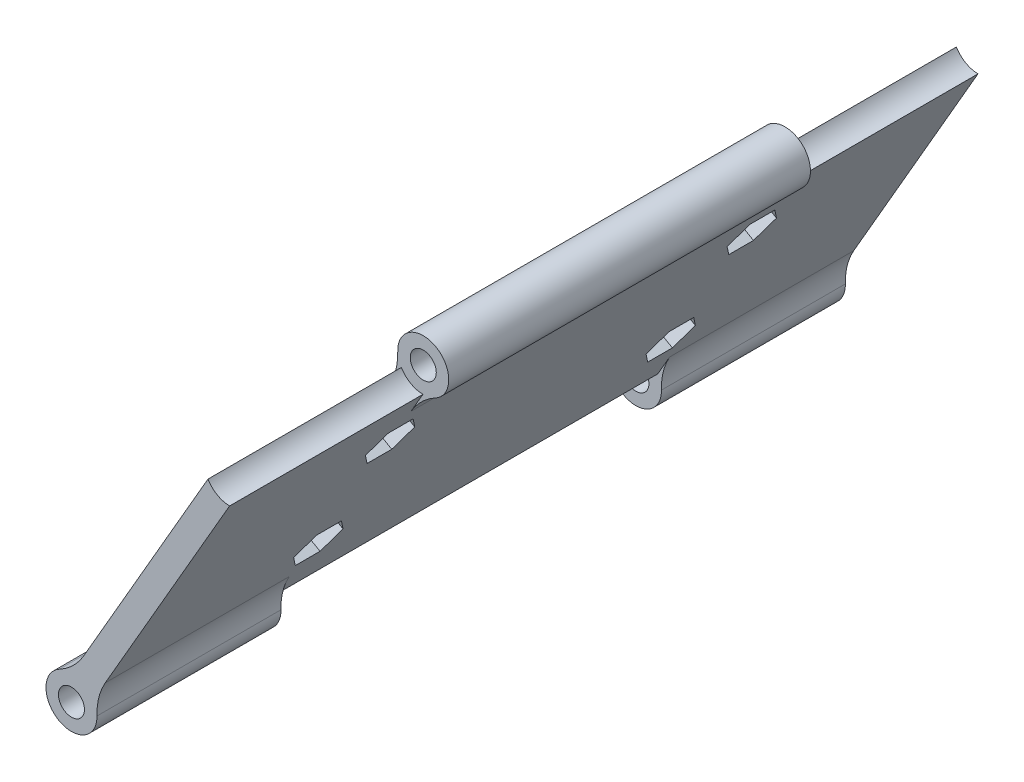
SolidWorks part; units mm, degrees
material "PLA"
ref_plane "Front Plane" through (0, 0, 0) normal (0, 0, 1) x (1, 0, 0)
ref_plane "Top Plane" through (0, 0, 0) normal (0, 1, 0) x (1, 0, 0)
ref_plane "Right Plane" through (0, 0, 0) normal (1, 0, 0) x (0, 0, -1)
sketch "Sketch2" plane through (0, 0, 0) normal (0, 0, 1) x (1, 0, 0)
  line L0 (0, 0) -> (38.1, 0)
  line L1 (0, 0) -> (0, -38.1)
  circle A0 centre (0, 0) radius 38.1
  circle A1 centre (0, -29.337) radius 1.5875
  circle A2 centre (-25.4066, 14.6685) radius 1.5875
  circle A3 centre (25.4066, 14.6685) radius 1.5875
  point P13 (0, 0)
  dimension "D1" = 76.2
  dimension "D2" = 3.175
  dimension "D3" = 8.763
  dimension "D4" = 3
extrude "Boss-Extrude1" add sketch "Sketch2" along normal blind 10 contours A1 L1 L0 A0 A3 A2 | A1 L1 A0 L0
sketch "Sketch3" plane through (0, 0, 10) normal (0, 0, 1) x (1, 0, 0)
  line L1 (0, -29.337) -> (25.4066, 14.6685)
  line L2 (1.7321, -30.337) -> (27.1386, 13.6685)
  line L3 (-1.7321, -28.337) -> (23.6745, 15.6685)
  circle A11 centre (0, -29.337) radius 1.5875
  circle A12 centre (25.4066, 14.6685) radius 1.5875
  circle A17 centre (0, -29.337) radius 2.0875
  circle A18 centre (25.4066, 14.6685) radius 2.0875
  circle A19 centre (0, -29.337) radius 4.0875
  circle A20 centre (25.4066, 14.6685) radius 4.0875
  dimension "D1" = 0.5
  dimension "D2" = 2
  dimension "D4" = 2
  dimension "D5" = 2
extrude "Boss-Extrude2" add sketch "Sketch3" along normal blind 120 separate body contours L2 A20 L3 A18 | L1 A20 L2 A18 | L3 A20 L1 A18 | A20 L1 A19 L2 | A20 L3 A19 L1 | L1 A19 L3 A17 | L2 A19 L1 A17 | L3 A19 L2 A17
delete or keep bodies "Body-Delete/Keep 2" type delete bodies bodies 101
ref_plane "Plane1" through (0, 0, 70) normal (0, 0, 1) x (1, 0, 0)
sketch "Sketch4" plane through (0, 0, 70) normal (0, 0, 1) x (1, 0, 0)
  circle A1 centre (0, -29.337) radius 4.0875
extrude "Cut-Extrude1" cut sketch "Sketch4" against normal blind 30.5 and the other way blind 30.5
sketch "Sketch5" plane through (0, 0, 10) normal (0, 0, -1) x (-1, 0, 0)
  circle A0 centre (-25.4066, 14.6685) radius 4.0875
extrude "Cut-Extrude2" cut sketch "Sketch5" against normal offset from surface (31 mm away) 1.5 up to face at (2.0875, -29.337, 39.5) offset beyond the face yes
sketch "Sketch6" plane through (0, 0, 130) normal (0, 0, 1) x (1, 0, 0)
  circle A0 centre (25.4066, 14.6685) radius 4.0875
extrude "Cut-Extrude3" cut sketch "Sketch6" against normal offset from surface (31 mm away) 1.5 contours A0 up to face at (2.0875, -29.337, 100.5) offset beyond the face yes
fillet "Fillet1" radius 10 6 edges at (21.8921, 12.5813, 70) (0.0503, -25.2498, 24.75) (0.0503, -25.2498, 115.25) (3.5144, -27.2498, 115.25) (3.5144, -27.2498, 24.75) (25.3562, 10.5813, 70)
sketch "Sketch7" plane through (10.9712, -6.3342, 0) normal (-0.866, 0.5, 0) x (0, 0, 1)
  circle A0 centre (40.9814, 11.2661) radius 1.5
  circle A1 centre (42.4851, -11.7339) radius 1.5
  circle A2 centre (98.9814, -11.7339) radius 1.5
  circle A3 centre (98.9814, 11.2661) radius 1.5
  circle A4 centre (40.9814, 11.2661) radius 2
  circle A5 centre (42.4851, -11.7339) radius 2
  circle A6 centre (98.9814, -11.7339) radius 2
  circle A7 centre (98.9814, 11.2661) radius 2
  dimension "D1" = 0.5
extrude "Cut-Extrude4" cut sketch "Sketch7" against normal up to surface (4 mm away) contours A4 | A7 | A6 | A5 up to face at (14.7532, -7.7836, 70)
sketch "Sketch8" plane through (14.4353, -8.3342, 0) normal (0.866, -0.5, 0) x (0, 0, -1)
  line L1 (-37.0219, 11.2661) -> (-39.0016, 14.6951)
  line L2 (-39.0016, 14.6951) -> (-42.9611, 14.6951)
  line L3 (-42.9611, 14.6951) -> (-44.9408, 11.2661)
  line L4 (-44.9408, 11.2661) -> (-42.9611, 7.8371)
  line L5 (-42.9611, 7.8371) -> (-39.0016, 7.8371)
  line L6 (-39.0016, 7.8371) -> (-37.0219, 11.2661)
  line L7 (-38.5256, -11.7339) -> (-40.5053, -8.3049)
  line L8 (-40.5053, -8.3049) -> (-44.4648, -8.3049)
  line L9 (-44.4648, -8.3049) -> (-46.4445, -11.7339)
  line L10 (-46.4445, -11.7339) -> (-44.4648, -15.1629)
  line L11 (-44.4648, -15.1629) -> (-40.5053, -15.1629)
  line L12 (-40.5053, -15.1629) -> (-38.5256, -11.7339)
  line L13 (-95.0219, 11.2661) -> (-97.0016, 14.6951)
  line L14 (-97.0016, 14.6951) -> (-100.9611, 14.6951)
  line L15 (-100.9611, 14.6951) -> (-102.9408, 11.2661)
  line L16 (-102.9408, 11.2661) -> (-100.9611, 7.8371)
  line L17 (-100.9611, 7.8371) -> (-97.0016, 7.8371)
  line L18 (-97.0016, 7.8371) -> (-95.0219, 11.2661)
  line L19 (-95.0219, -11.7339) -> (-97.0016, -8.3049)
  line L20 (-97.0016, -8.3049) -> (-100.9611, -8.3049)
  line L21 (-100.9611, -8.3049) -> (-102.9408, -11.7339)
  line L22 (-102.9408, -11.7339) -> (-100.9611, -15.1629)
  line L23 (-100.9611, -15.1629) -> (-97.0016, -15.1629)
  line L24 (-97.0016, -15.1629) -> (-95.0219, -11.7339)
  circle A0 centre (-40.9814, 11.2661) radius 3.429 construction
  circle A1 centre (-42.4851, -11.7339) radius 3.429 construction
  circle A2 centre (-98.9814, 11.2661) radius 3.429 construction
  circle A3 centre (-98.9814, -11.7339) radius 3.429 construction
  dimension "D1" = 6.858
extrude "Cut-Extrude5" cut sketch "Sketch8" against normal blind 2
